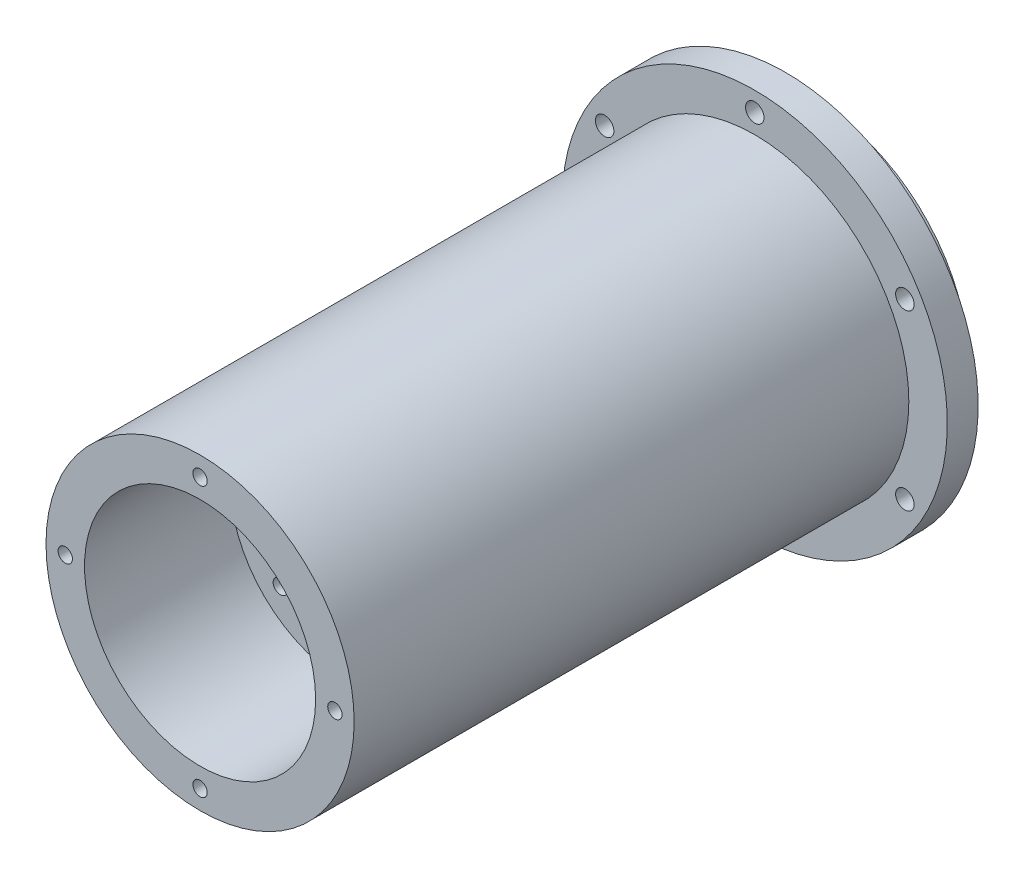
SolidWorks part; units mm, degrees
material "1060 Alloy"
ref_plane "Front Plane" through (0, 0, 0) normal (0, 0, 1) x (1, 0, 0)
ref_plane "Top Plane" through (0, 0, 0) normal (0, 1, 0) x (1, 0, 0)
ref_plane "Right Plane" through (0, 0, 0) normal (1, 0, 0) x (0, 0, -1)
sketch "Sketch1" plane through (0, 0, 0) normal (0, 0, 1) x (1, 0, 0)
  circle A0 centre (0, 0) radius 31.75
  dimension "D1" = 63.5
extrude "Boss-Extrude1" add sketch "Sketch1" along normal mid plane 101.6
sketch "Sketch2" plane through (0, 0, -50.8) normal (0, 0, -1) x (-1, 0, 0)
  circle A0 centre (0, 0) radius 25.0825
  circle A1 centre (0, 0) radius 31.75
  circle A2 centre (0, 0) radius 31.75 construction
  point P4 (31.75, 0)
  dimension "D1" = 50.165
extrude "Cut-Extrude1" cut sketch "Sketch2" against normal blind 5.08
sketch "Sketch3" plane through (0, 0, -50.8) normal (0, 0, -1) x (-1, 0, 0)
  circle A0 centre (0, 0) radius 22.5425
  circle A1 centre (0, 0) radius 25.0825 construction
  dimension "D1" = 2.54
extrude "Cut-Extrude2" cut sketch "Sketch3" against normal offset from surface (71.247 mm away) 30.353 up to face at (31.75, 0, 50.8)
sketch "Sketch4" plane through (0, 0, 50.8) normal (0, 0, 1) x (1, 0, 0)
  circle A0 centre (0, 0) radius 25.4
  circle A1 centre (0, 0) radius 31.75 construction
  circle A2 centre (0, 0) radius 31.75
  dimension "D1" = 50.8
extrude "Cut-Extrude3" cut sketch "Sketch4" against normal offset from surface (91.44 mm away) 5.08 up to face at (-25.0825, 0, -45.72)
sketch "Sketch5" plane through (0, 0, 50.8) normal (0, 0, 1) x (1, 0, 0)
  circle A0 centre (0, 0) radius 19.05
  dimension "D1" = 38.1
extrude "Cut-Extrude4" cut sketch "Sketch5" against normal blind 24.003
sketch "Sketch6" plane through (0, 0, 26.797) normal (0, 0, 1) x (1, 0, 0)
  circle A0 centre (0, 0) radius 9.6266
  dimension "D1" = 19.2532
extrude "Cut-Extrude5" cut sketch "Sketch6" against normal through all
sketch "Sketch8" plane through (0, 0, -40.64) normal (0, 0, 1) x (1, 0, 0)
  circle A0 centre (0, 0) radius 28.575 construction
  circle A1 centre (0, 28.575) radius 1.524
  dimension "D1" = 57.15
  dimension "D2" = 3.048
extrude "Cut-Extrude6" cut sketch "Sketch8" against normal through all
pattern_circular "CirPattern1" count 6 over 360 about axis through (0, 0, 0) along (0, 0, 1) of "Cut-Extrude6"
sketch "Sketch9" plane through (0, 0, 50.8) normal (0, 0, 1) x (1, 0, 0)
  line L0 (0, -34.925) -> (0, 34.925) construction
  circle A0 centre (0, 0) radius 22.225 construction
  circle A1 centre (0, 22.225) radius 1.1811
  dimension "D1" = 44.45
  dimension "D2" = 2.3622
extrude "Cut-Extrude7" cut sketch "Sketch9" against normal blind 12.7
pattern_circular "CirPattern2" count 4 over 360 about axis through (0, 0, 0) along (0, 0, 1) of "Cut-Extrude7"
sketch "Sketch10" plane through (0, 0, 26.797) normal (0, 0, 1) x (1, 0, 0)
  circle A0 centre (0, 0) radius 11.303
  dimension "D1" = 22.606
extrude "Cut-Extrude8" cut sketch "Sketch10" against normal blind 1.397
sketch "Sketch11" plane through (0, 0, 26.797) normal (0, 0, 1) x (1, 0, 0)
  line L0 (-10.7763, 10.7763) -> (0, 0) construction
  line L1 (0, 0) -> (-15.24, 0) construction
  circle A0 centre (0, 0) radius 15.24 construction
  circle A1 centre (-10.7763, 10.7763) radius 1.1811
  dimension "D1" = 30.48
  dimension "D3" = 2.3622
  dimension "D2" = 45
extrude "Cut-Extrude9" cut sketch "Sketch11" against normal through all
pattern_circular "CirPattern3" count 4 over 360 about axis through (0, 0, 0) along (0, 0, 1) of "Cut-Extrude9"
